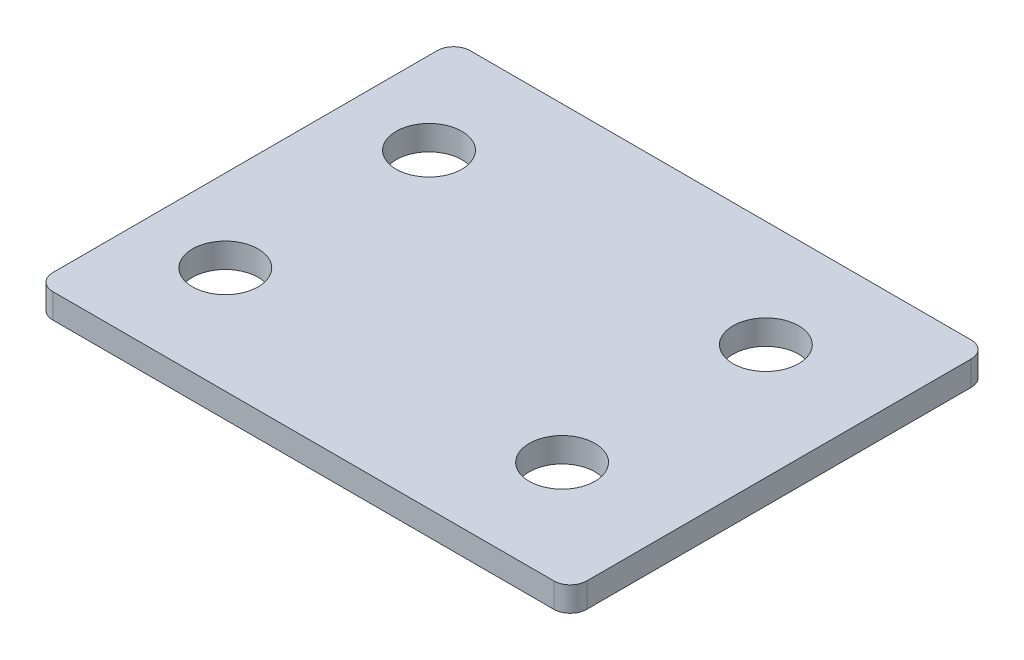
SolidWorks part; units mm, degrees
ref_plane "Front Plane" through (0, 0, 0) normal (0, 0, 1) x (1, 0, 0)
ref_plane "Top Plane" through (0, 0, 0) normal (0, 1, 0) x (1, 0, 0)
ref_plane "Right Plane" through (0, 0, 0) normal (1, 0, 0) x (0, 0, -1)
sketch "Sketch1" plane through (0, 0, 0) normal (0, 1, 0) x (1, 0, 0)
  line L1 (-30.5, -25.4) -> (30.5, -25.4)
  line L2 (-32.5, -23.4) -> (-32.5, 23.4)
  line L3 (-30.5, 25.4) -> (30.5, 25.4)
  line L4 (32.5, -23.4) -> (32.5, 23.4)
  line L5 (-32.5, -25.4) -> (32.5, 25.4) construction
  line L6 (-32.5, 25.4) -> (32.5, -25.4) construction
  circle A0 centre (-22.5, 12.4) radius 4
  circle A1 centre (18.5, 12.4) radius 4
  circle A2 centre (-22.5, -12.4) radius 4
  circle A3 centre (18.5, -12.4) radius 4
  arc A4 (-32.5, -23.4) -> (-30.5, -25.4) centre (-30.5, -23.4) ccw
  arc A5 (30.5, -25.4) -> (32.5, -23.4) centre (30.5, -23.4) ccw
  arc A6 (32.5, 23.4) -> (30.5, 25.4) centre (30.5, 23.4) ccw
  arc A7 (-32.5, 23.4) -> (-30.5, 25.4) centre (-30.5, 23.4) cw
  point P0 (0, 0)
  dimension "D3" = 8
  dimension "D5" = 8
  dimension "D6" = 8
  dimension "D7" = 8
  dimension "D15" = 2
  dimension "D1" = 65
  dimension "D2" = 50.8
  dimension "D4" = 10
  dimension "D8" = 10
  dimension "D9" = 13
  dimension "D10" = 13
  dimension "D11" = 13
  dimension "D12" = 13
  dimension "D13" = 14
  dimension "D14" = 14
extrude "Boss-Extrude1" add sketch "Sketch1" along normal blind 3
